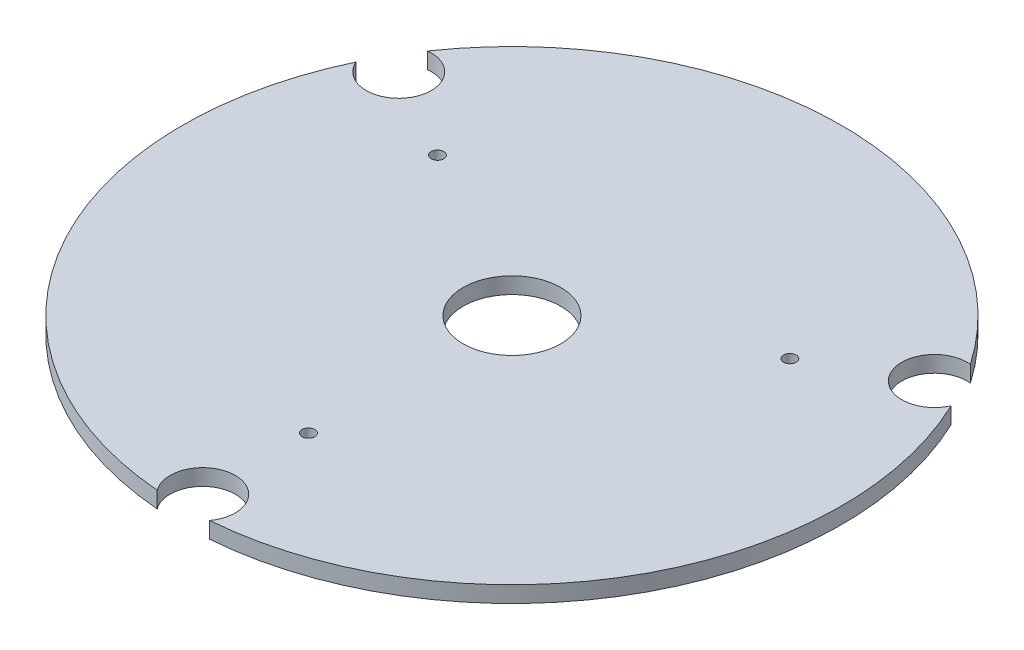
SolidWorks part; units mm, degrees
ref_plane "Front Plane" through (0, 0, 0) normal (0, 0, 1) x (1, 0, 0)
ref_plane "Top Plane" through (0, 0, 0) normal (0, 1, 0) x (1, 0, 0)
ref_plane "Right Plane" through (0, 0, 0) normal (1, 0, 0) x (0, 0, -1)
sketch "Sketch1" plane through (0, 0, 0) normal (0, 1, 0) x (1, 0, 0)
  line L0 (0, 0) -> (0, 92.6435) construction
  line L1 (0, 0) -> (92.252, 53.2617) construction
  circle A0 centre (0, 0) radius 81
  circle A1 centre (43.3013, 25) radius 1.55
  circle A2 centre (0, -50) radius 1.55
  circle A3 centre (-43.3013, 25) radius 1.55
  circle A4 centre (0, 0) radius 12
  dimension "D1" = 162
  dimension "D3" = 3.1
  dimension "D7" = 50
  dimension "D8" = 24
  dimension "D2" = 60
  dimension "D4" = 50
  dimension "D6" = 50
  dimension "D5" = 3
extrude "Boss-Extrude1" add sketch "Sketch1" along normal mid plane 4
sketch "Sketch2" plane through (0, -2, 0) normal (0, -1, 0) x (1, 0, 0)
  arc A0 (-68.3738, -43.4284) -> (-71.797, -37.4992) centre (-65.8179, -38) ccw construction
  arc A1 (-68.3738, -43.4284) -> (-71.797, -37.4992) centre (-65.8179, -38) ccw construction
  arc A2 (-66.7048, -45.9507) -> (-73.1469, -34.7927) centre (-65.8179, -38) ccw
  circle A3 centre (0, 0) radius 81 construction
  arc A4 (66.7048, -45.9507) -> (73.1469, -34.7927) centre (0, 0) ccw
  arc A5 (-69.2257, -45.2379) -> (-73.79, -37.3323) centre (-65.8179, -38) ccw construction
  arc A7 (-6.442, 80.7434) -> (6.442, 80.7434) centre (0, 76) ccw
  arc A8 (73.1469, -34.7927) -> (66.7048, -45.9507) centre (65.8179, -38) ccw
  arc A10 (6.442, 80.7434) -> (-6.442, 80.7434) centre (0, 0) ccw
  arc A11 (-73.1469, -34.7927) -> (-66.7048, -45.9507) centre (0, 0) ccw
  dimension "D1" = 2
  dimension "D2" = 3
extrude "Cut-Extrude1" cut sketch "Sketch2" against normal through all
